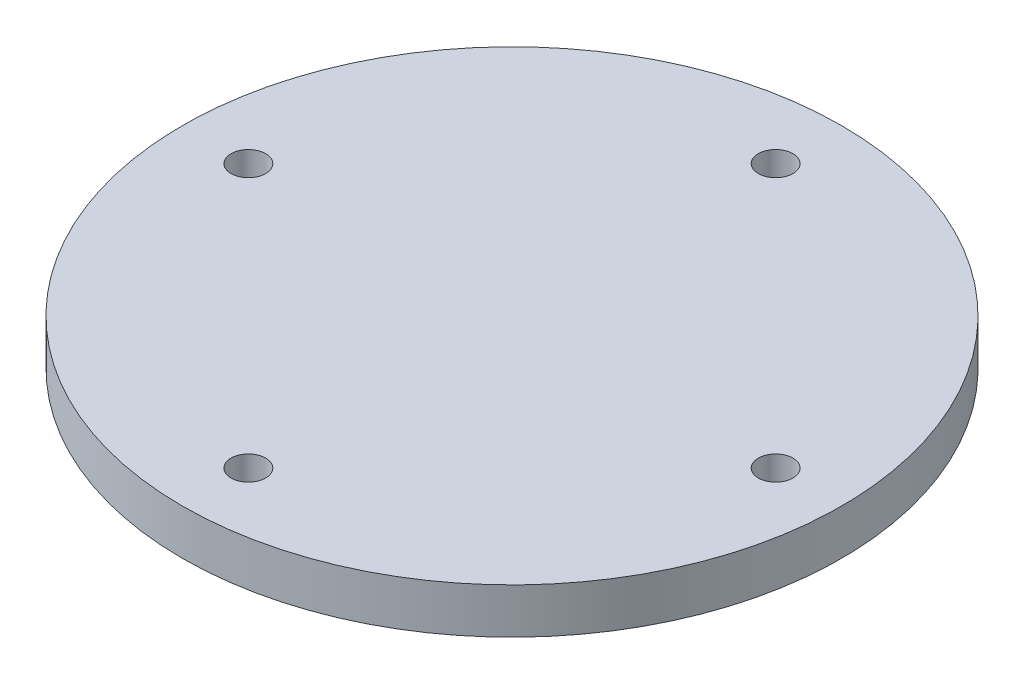
SolidWorks part; units mm, degrees
ref_plane "Front" through (0, 0, 0) normal (0, 0, 1) x (1, 0, 0)
ref_plane "Top" through (0, 0, 0) normal (0, 1, 0) x (1, 0, 0)
ref_plane "Right" through (0, 0, 0) normal (1, 0, 0) x (0, 0, -1)
sketch "Sketch2" plane through (0, 0, 0) normal (0, 1, 0) x (1, 0, 0)
  circle A0 centre (0, 0) radius 50.8
  dimension "D1" = 101.6
extrude "Boss-Extrude1" add sketch "Sketch2" along normal blind 6.985
sketch "Sketch3" plane through (0, 6.985, 0) normal (0, 1, 0) x (1, 0, 0)
  circle A2 centre (0, -40.64) radius 2.667
  circle A3 centre (0, 0) radius 40.64
  circle A4 centre (0, 0) radius 40.64 construction
  circle A5 centre (-40.64, 0) radius 2.667
  circle A6 centre (0, 40.64) radius 2.667
  circle A7 centre (40.64, 0) radius 2.667
  circle A8 centre (0, 0) radius 50.8 construction
  dimension "D2" = 5.334
  dimension "D1" = 10.16
  dimension "D3" = 4
extrude "Cut-Extrude1" cut sketch "Sketch3" against normal through all
